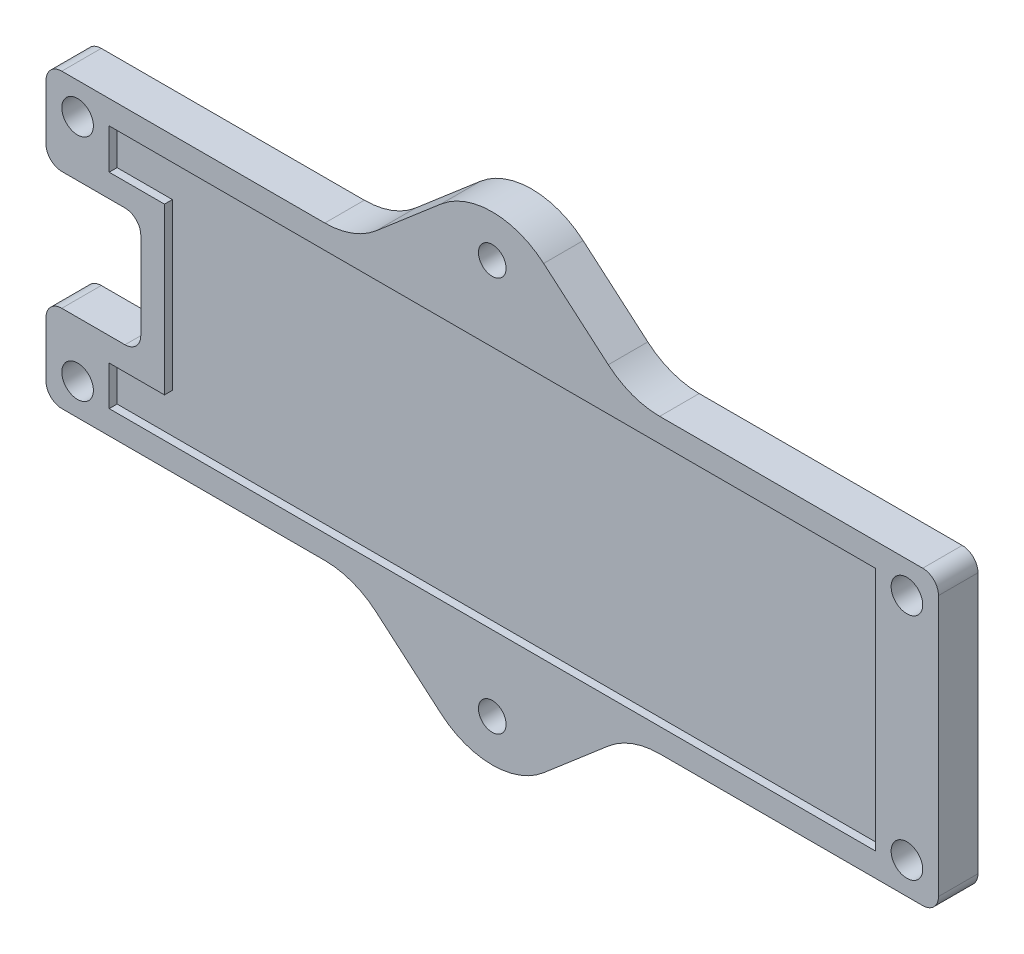
SolidWorks part; units mm, degrees
material "瞎编数据的PLA"
ref_plane "前视基准面" through (0, 0, 0) normal (0, 0, 1) x (1, 0, 0)
ref_plane "上视基准面" through (0, 0, 0) normal (0, 1, 0) x (1, 0, 0)
ref_plane "右视基准面" through (0, 0, 0) normal (1, 0, 0) x (0, 0, -1)
sketch "草图1" plane through (0, 0, 0) normal (0, 0, 1) x (1, 0, 0)
  line L0 (-56.5, 18.5) -> (56.5, 18.5)
  line L1 (-52.5, 14.5) -> (52.5, 14.5) construction
  line L2 (-52.5, 14.5) -> (-52.5, -14.5) construction
  line L3 (-52.5, -14.5) -> (52.5, -14.5) construction
  line L4 (52.5, 14.5) -> (52.5, -14.5) construction
  line L5 (-52.5, 14.5) -> (52.5, -14.5) construction
  line L6 (-52.5, -14.5) -> (52.5, 14.5) construction
  line L7 (56.5, 18.5) -> (56.5, -18.5)
  line L8 (-56.5, -18.5) -> (56.5, -18.5)
  line L9 (-56.5, 18.5) -> (-56.5, -18.5)
  circle A0 centre (52.5, 14.5) radius 2
  circle A1 centre (52.5, -14.5) radius 2
  circle A2 centre (-52.5, -14.5) radius 2
  circle A3 centre (-52.5, 14.5) radius 2
  point P0 (0, 0)
  dimension "D1" = 4
  dimension "D2" = 105
  dimension "D3" = 29
  dimension "D4" = 4
extrude "凸台-拉伸1" add sketch "草图1" along normal mid plane 5
sketch "草图2" plane through (0, 0, -2.5) normal (0, 0, -1) x (-1, 0, 0)
  line L0 (56.5, 0) -> (-56.5, 0) construction
  line L1 (56.5, 18.5) -> (56.5, -18.5) construction
  line L2 (-56.5, -18.5) -> (-56.5, 18.5) construction
  line L3 (56.5, -7.5) -> (44.5, -7.5)
  line L4 (44.5, -7.5) -> (44.5, 7.5)
  line L5 (44.5, 7.5) -> (56.5, 7.5)
  line L6 (56.5, 7.5) -> (56.5, -7.5)
  dimension "D1" = 15
  dimension "D2" = 12
extrude "切除-拉伸1" cut sketch "草图2" against normal through all
sketch "草图3" plane through (0, 0, -2.5) normal (0, 0, -1) x (-1, 0, 0)
  line L0 (-48.5, -15.5) -> (48.5001, -15.5)
  line L1 (48.5269, 15.5) -> (-48.5, 15.5)
  line L2 (41.5, -10.5) -> (41.5, 10.4207)
  line L3 (48.5001, -15.5) -> (48.5001, -10.5)
  line L4 (48.5001, 10.4207) -> (48.5269, 15.5)
  line L5 (-48.5, 15.5) -> (-48.5, -15.5)
  line L6 (48.5001, -10.5) -> (41.5, -10.5)
  line L7 (41.5, 10.4207) -> (48.5001, 10.4207)
  line L8 (56.5, 18.5) -> (56.5, 7.5) construction
  line L9 (-56.5, 18.5) -> (56.5, 18.5) construction
  line L10 (44.5, 0) -> (-56.5, 0) construction
  line L11 (44.5, 7.5) -> (44.5, -7.5) construction
  line L12 (-56.5, -18.5) -> (-56.5, 18.5) construction
  dimension "D1" = 7.9731
  dimension "D2" = 7.9999
  dimension "D3" = 15
  dimension "D4" = 105
  dimension "D5" = 3
  dimension "D6" = 8.0793
  dimension "D7" = 29
  dimension "D8" = 34
extrude "切除-拉伸2" cut sketch "草图3" against normal blind 1
fillet "圆角1" radius 2 8 edges at (48.5, 15.5, -2) (48.5, -15.5, -2) (-48.5001, -15.5, -2) (-41.5, -10.5, -2) (-48.5001, -10.5, -2) (-48.5269, 15.5, -2) (-48.5001, 10.4207, -2) (-41.5, 10.4207, -2)
fillet "圆角2" radius 2 8 edges at (56.5, 18.5, 0) (56.5, -18.5, 0) (-56.5, -18.5, 0) (-44.5, -7.5, 0) (-56.5, -7.5, 0) (-56.5, 7.5, 0) (-44.5, 7.5, 0) (-56.5, 18.5, 0)
sketch "草图4" plane through (0, 0, -2.5) normal (0, 0, -1) x (-1, 0, 0)
  line L0 (0, 55.0971) -> (0, -44.7473) construction
  line L1 (44.5, 0) -> (-56.5, 0) construction
  line L2 (44.5, 5.5) -> (44.5, -5.5) construction
  line L3 (-56.5, -16.5) -> (-56.5, 16.5) construction
  line L4 (17.5, 18.5) -> (0, 33.5)
  line L5 (-54.5, 18.5) -> (54.5, 18.5) construction
  line L6 (-17.5, 18.5) -> (17.5, 18.5)
  line L7 (-17.5, 18.5) -> (0, 33.5)
  line L8 (54.5, -18.5) -> (-54.5, -18.5) construction
  line L9 (17.5, -18.5) -> (-17.5, -18.5)
  line L10 (-17.5, -18.5) -> (0, -33.5)
  line L11 (17.5, -18.5) -> (0, -33.5)
  dimension "D1" = 35
  dimension "D2" = 15
extrude "凸台-拉伸2" add sketch "草图4" against normal blind 5
fillet "圆角3" radius 10 6 edges at (-17.5, -18.5, 0) (17.5, -18.5, 0) (0, -33.5, 0) (0, 33.5, 0) (17.5, 18.5, 0) (-17.5, 18.5, 0)
sketch "草图5" plane through (0, 0, -2.5) normal (0, 0, -1) x (-1, 0, 0)
  line L0 (0, 38.8115) -> (0, -49.009) construction
  line L1 (0, 0) -> (51.0596, 0) construction
  circle A0 centre (0, -25) radius 1.75
  circle A1 centre (0, 25) radius 1.75
  dimension "D1" = 3.5
  dimension "D2" = 25
extrude "切除-拉伸3" cut sketch "草图5" against normal through all
mirror "镜向1" about plane through (0, 0, 0) normal (0, 0, 1) of "切除-拉伸2"
